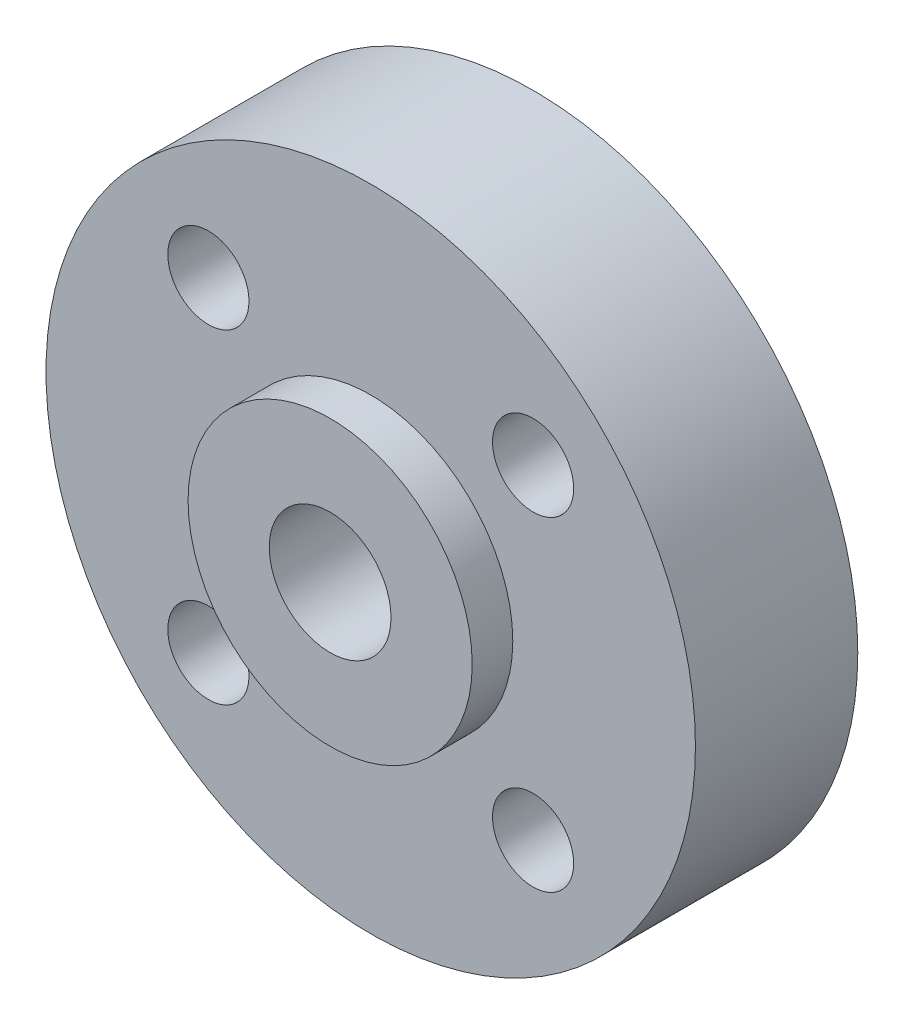
SolidWorks part; units mm, degrees
material "AISI 304"
ref_plane "前视基准面" through (0, 0, 0) normal (0, 0, 1) x (1, 0, 0)
ref_plane "上视基准面" through (0, 0, 0) normal (0, 1, 0) x (1, 0, 0)
ref_plane "右视基准面" through (0, 0, 0) normal (1, 0, 0) x (0, 0, -1)
sketch "草图1" plane through (0, 0, 0) normal (0, 0, 1) x (1, 0, 0)
  circle A0 centre (0, 0) radius 16
extrude "凸台-拉伸1" add sketch "草图1" along normal blind 8
sketch "草图2" plane through (0, 0, 8) normal (0, 0, 1) x (1, 0, 0)
  circle A0 centre (0, 0) radius 7
extrude "凸台-拉伸2" add sketch "草图2" along normal blind 2
sketch "草图3" plane through (0, 0, 8) normal (0, 0, 1) x (1, 0, 0)
  line L1 (-8, 8) -> (8, 8) construction
  line L2 (-8, 8) -> (-8, -8) construction
  line L3 (-8, -8) -> (8, -8) construction
  line L4 (8, 8) -> (8, -8) construction
  line L5 (-8, 8) -> (8, -8) construction
  line L6 (-8, -8) -> (8, 8) construction
  circle A0 centre (-8, 8) radius 2
  circle A1 centre (8, 8) radius 2
  circle A2 centre (8, -8) radius 2
  circle A3 centre (-8, -8) radius 2
  point P0 (0, 0)
extrude "切除-拉伸1" cut sketch "草图3" against normal blind 20
sketch "草图4" plane through (0, 0, 10) normal (0, 0, 1) x (1, 0, 0)
  circle A0 centre (0, 0) radius 3
extrude "切除-拉伸2" cut sketch "草图4" against normal blind 20
